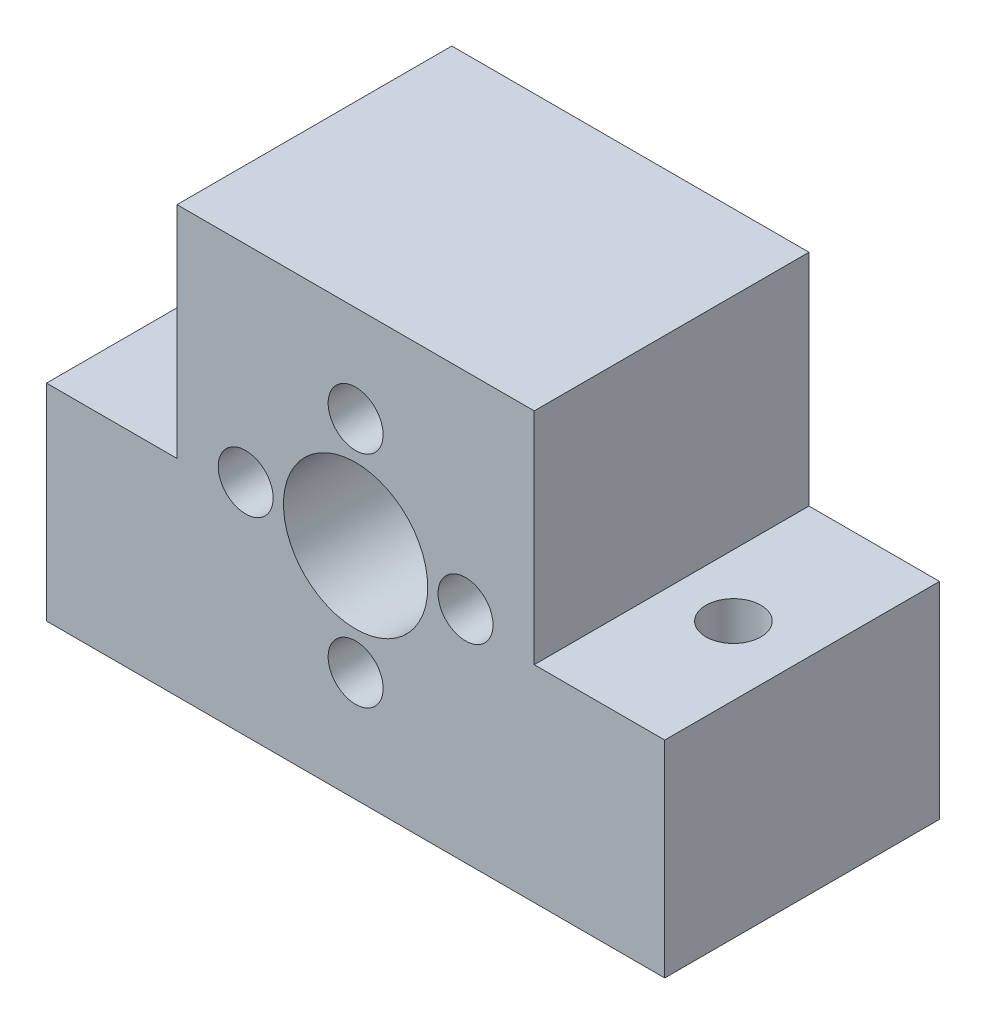
SolidWorks part; units mm, degrees
ref_plane "Front Plane" through (0, 0, 0) normal (0, 0, 1) x (1, 0, 0)
ref_plane "Top Plane" through (0, 0, 0) normal (0, 1, 0) x (1, 0, 0)
ref_plane "Right Plane" through (0, 0, 0) normal (1, 0, 0) x (0, 0, -1)
sketch "Sketch1" plane through (0, 0, 0) normal (0, 0, 1) x (1, 0, 0)
  line L0 (0, -438.3722) -> (0, 21480.2356) construction
  line L1 (-438.3722, 0) -> (21480.2356, 0) construction
  line L3 (-22.5, -16) -> (22.5, -16)
  line L4 (-22.5, -16) -> (-22.5, 15)
  line L5 (-22.5, 15) -> (22.5, 15)
  line L6 (22.5, -16) -> (22.5, 15)
  circle A0 centre (0, 0) radius 5.25
  circle A1 centre (0, 0) radius 8 construction
  circle A2 centre (0, 8) radius 2
  circle A3 centre (8, 0) radius 2
  circle A4 centre (0, -8) radius 2
  circle A5 centre (-8, 0) radius 2
  point P4 (0, 0)
  point P24 (0, 0)
  dimension "D2" = 10.5
  dimension "D4" = 16
  dimension "D5" = 4
  dimension "D7" = 8
  dimension "D8" = 8
  dimension "D1" = 15
  dimension "D3" = 45
  dimension "D9" = 16
  dimension "D10" = 22.5
  dimension "D6" = 4
extrude "Boss-Extrude1" add sketch "Sketch1" along normal blind 20
sketch "Sketch2" plane through (0, 15, 0) normal (0, 1, 0) x (1, 0, 0)
  line L0 (0, -1000) -> (0, 49000) construction
  line L1 (-1030, -10) -> (48970, -10) construction
  line L2 (-22.5, -20) -> (-22.5, 0) construction
  circle A0 centre (-17.5, -10) radius 2
  circle A1 centre (17.5, -10) radius 2
  point P8 (-22.5, -10)
  dimension "D2" = 4
  dimension "D1" = 5
extrude "Cut-Extrude1" cut sketch "Sketch2" against normal through all
sketch "Sketch3" plane through (0, 0, 0) normal (0, 0, -1) x (-1, 0, 0)
  line L0 (0, -1000) -> (0, 49000) construction
  line L1 (-1000, 0) -> (49000, 0) construction
  line L2 (-22.5, 15) -> (22.5, 15) construction
  line L3 (22.5, -16) -> (13, -16)
  line L4 (22.5, -16) -> (22.5, 15)
  line L5 (22.5, 15) -> (13, 15)
  line L6 (13, -16) -> (13, 15)
  line L7 (22.5, -1) -> (13, -1)
  line L8 (-22.5, -1) -> (-13, -1)
  line L9 (-13, -16) -> (-13, 15)
  line L10 (-22.5, 15) -> (-13, 15)
  line L11 (-22.5, -16) -> (-22.5, 15)
  line L12 (-22.5, -16) -> (-13, -16)
  line M7 (-22.5, 15) -> (-22.5, -16)
  line M10 (22.5, 15) -> (-22.5, 15)
  dimension "D1" = 13
  dimension "D2" = 15
extrude "Cut-Extrude2" cut sketch "Sketch3" against normal through all contours L7 L4 L6 M10 | L8 L9 M10 M7
